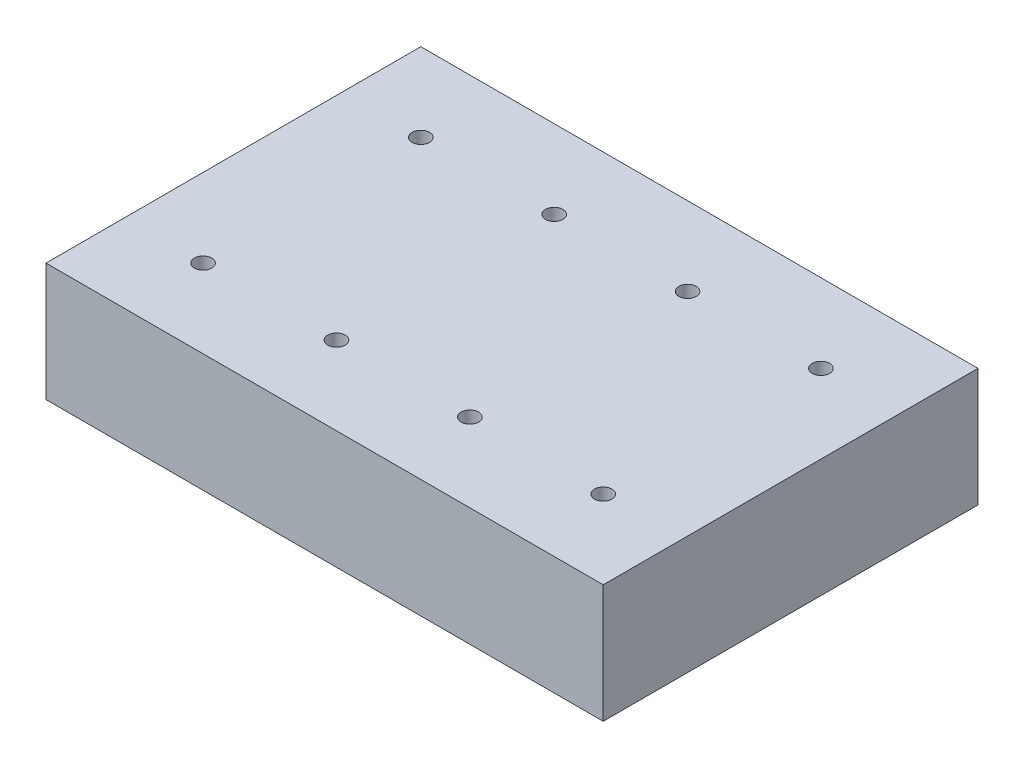
SolidWorks part; units mm, degrees
ref_plane "Front Plane" through (0, 0, 0) normal (0, 0, 1) x (1, 0, 0)
ref_plane "Top Plane" through (0, 0, 0) normal (0, 1, 0) x (1, 0, 0)
ref_plane "Right Plane" through (0, 0, 0) normal (1, 0, 0) x (0, 0, -1)
other "Graphic1"
sketch "Sketch1" plane through (0, 0, 0) normal (0, 1, 0) x (1, 0, 0)
  line L1 (-312.706, 132.0167) -> (-185.006, 132.0167)
  line L2 (-312.706, 132.0167) -> (-312.706, 46.1167)
  line L3 (-312.706, 46.1167) -> (-185.006, 46.1167)
  line L4 (-185.006, 132.0167) -> (-185.006, 46.1167)
  dimension "D1" = 85.9
  dimension "D2" = 127.7
extrude "Boss-Extrude1" add sketch "Sketch1" along normal blind 28.1
sketch "Sketch2" plane through (0, 0, 0) normal (0, -1, 0) x (-1, 0, 0)
  line L0 (312.706, 46.1167) -> (185.006, 46.1167) construction
  line L1 (312.706, 132.0167) -> (312.706, 46.1167) construction
  line L2 (185.006, 46.1167) -> (185.006, 132.0167) construction
  circle A0 centre (294.706, 64.1167) radius 13.9
  circle A1 centre (264.136, 64.1167) radius 13.9
  circle A2 centre (233.566, 64.1167) radius 13.9
  circle A3 centre (203.006, 64.1167) radius 13.9
  dimension "D1" = 18
  dimension "D3" = 27.8
  dimension "D4" = 18
  dimension "D7" = 30.56
  dimension "D2" = 18
  dimension "D5" = 18
  dimension "D6" = 91.7
sketch "Sketch3" plane through (0, 0, 0) normal (0, -1, 0) x (1, 0, 0)
  line L0 (-185.006, -132.0167) -> (-312.706, -132.0167) construction
  line L1 (-312.706, -132.0167) -> (-312.706, -46.1167) construction
  line L3 (-185.006, -46.1167) -> (-185.006, -132.0167) construction
  circle A0 centre (-233.566, -114.0167) radius 13.9
  circle A1 centre (-264.136, -114.0167) radius 13.9
  circle A2 centre (-294.706, -114.0167) radius 13.9
  circle A3 centre (-203.006, -114.0167) radius 13.9
  dimension "D1" = 18
  dimension "D3" = 18
  dimension "D4" = 18
  dimension "D7" = 30.57
  dimension "D2" = 18
  dimension "D5" = 18
  dimension "D6" = 30.57
  dimension "D8" = 30.56
  dimension "D9" = 18
extrude "Cut-Extrude3" cut sketch "Sketch2" against normal blind 25 contours A0 | A3 | A2 | A1
chamfer "Chamfer3" distance 1 angle 45 1 edges at (-264.136, 0, -78.0167)
chamfer "Chamfer4" distance 1 angle 45 3 edges at (-203.006, 0, -78.0167) (-233.566, 0, -78.0167) (-294.706, 0, -78.0167)
extrude "Cut-Extrude5" cut sketch "Sketch3" against normal blind 25 contours A0 | A3 | A1 | A2
chamfer "Chamfer5" distance 1 angle 45 4 edges at (-203.006, 0, -127.9167) (-233.566, 0, -127.9167) (-294.706, 0, -127.9167) (-264.136, 0, -127.9167)
chamfer "Chamfer6" distance 1 angle 45 4 edges at (-248.856, 0, -132.0167) (-185.006, 0, -89.0667) (-248.856, 0, -46.1167) (-312.706, 0, -89.0667)
sketch "Sketch5" plane through (0, 25, 0) normal (0, -1, 0) x (-1, 0, 0)
  line L0 (312.706, 46.1167) -> (185.006, 46.1167) construction
  line L1 (312.706, 132.0167) -> (312.706, 46.1167) construction
  circle A1 centre (294.706, 64.1167) radius 2
  circle A2 centre (264.136, 64.1167) radius 2
  circle A3 centre (233.566, 64.1167) radius 2
  circle A4 centre (203.006, 64.1167) radius 2
  circle A5 centre (294.706, 114.0167) radius 2
  circle A6 centre (264.136, 114.0167) radius 2
  circle A7 centre (233.566, 114.0167) radius 2
  circle A8 centre (203.006, 114.0167) radius 2
  point P10 (264.136, 64.1167)
  point P14 (233.566, 64.1167)
  point P18 (203.006, 64.1167)
  point P22 (294.706, 114.0167)
  point P26 (264.136, 114.0167)
  point P30 (233.566, 114.0167)
  point P34 (203.006, 114.0167)
  dimension "D1" = 18
  dimension "D2" = 18
extrude "Cut-Extrude7" cut sketch "Sketch5" against normal blind 10
